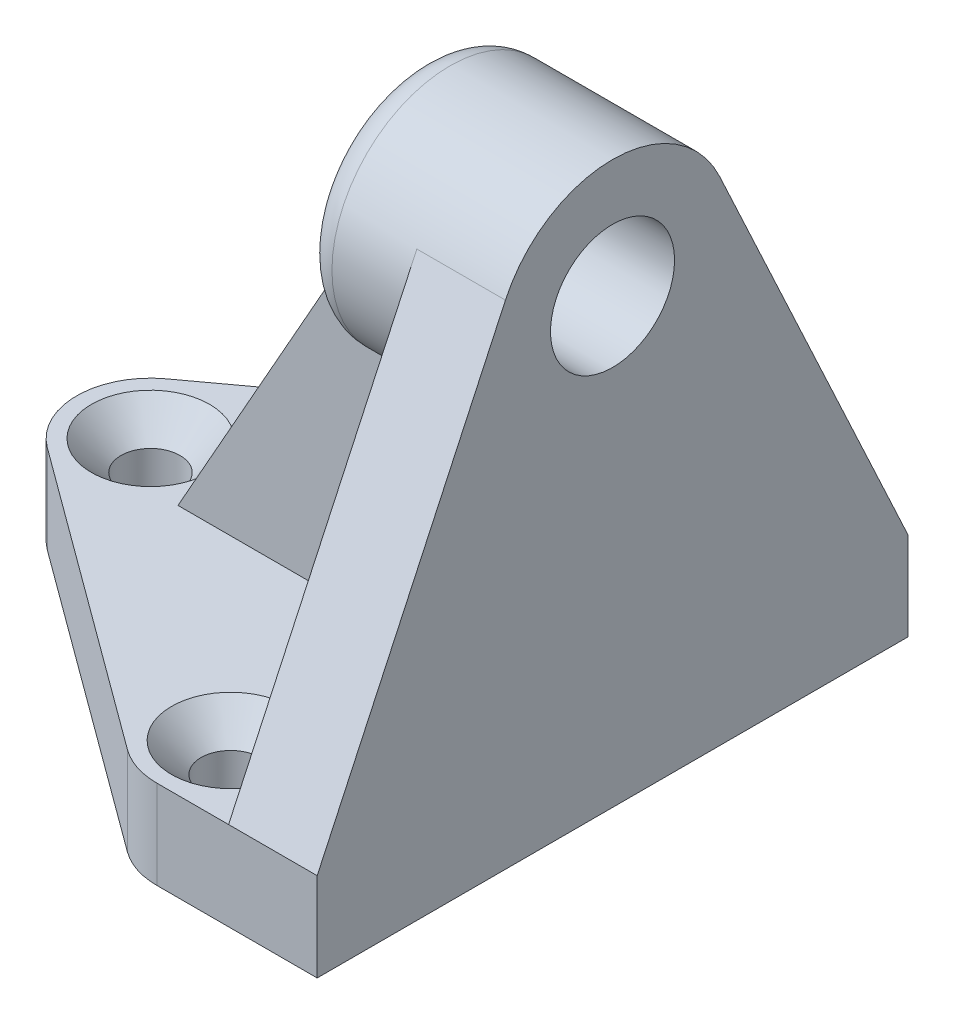
SolidWorks part; units mm, degrees
material "ABS"
ref_plane "Спереди" through (0, 0, 0) normal (0, 0, 1) x (1, 0, 0)
ref_plane "Сверху" through (0, 0, 0) normal (0, 1, 0) x (1, 0, 0)
ref_plane "Справа" through (0, 0, 0) normal (1, 0, 0) x (0, 0, -1)
other "Configuration Table"
sketch "Эскиз1" plane through (0, 0, 0) normal (0, 1, 0) x (1, 0, 0)
  line L0 (0, -20) -> (0, 20)
  line L4 (0, 0) -> (-50, 0) construction
  line L7 (0, -20) -> (-10.8613, -20)
  line L8 (0, 20) -> (-10.8613, 20)
  line L9 (-34.2466, -4.03) -> (-13.8208, -19.03)
  line L10 (-34.2466, 4.03) -> (-13.8208, 19.03)
  arc A1 (-34.2466, 4.03) -> (-34.2466, -4.03) centre (-31.2871, 0) ccw
  circle A4 centre (-31.2871, 0) radius 2
  circle A5 centre (-10.8613, -15) radius 2
  arc A6 (-10.8613, -20) -> (-13.8208, -19.03) centre (-10.8613, -15) cw
  arc A7 (-10.8613, 20) -> (-13.8208, 19.03) centre (-10.8613, 15) ccw
  circle A8 centre (-10.8613, 15) radius 2
  point P2 (0, 0)
  point P13 (-12.5, -20)
  point P16 (-12.5, 20)
  dimension "D3" = 12.5
  dimension "D4" = 5
  dimension "D6" = 5
  dimension "D7" = 4
  dimension "D8" = 4
  dimension "D9" = 5
  dimension "D10" = 4
  dimension "D11" = 10.8613
  dimension "D1" = 40
  dimension "D2" = 50
  dimension "D5" = 31.2871
extrude "Бобышка-Вытянуть1" add sketch "Эскиз1" along normal blind 6
chamfer "Фаска3" distance 2 angle 45 3 edges at (-10.8613, 6, 17) (-31.2871, 6, 2) (-10.8613, 6, -13)
sketch "Эскиз4" plane through (0, 0, 0) normal (1, 0, 0) x (0, 0, -1)
  line L0 (0, 0) -> (0, 53.5747) construction
  line L1 (-20, 0) -> (20, 0) construction
  line L2 (-45.2355, 6) -> (56.9604, 6) construction
  line L3 (-7.2523, 33.3769) -> (-20, 6)
  line L4 (-20, 6) -> (-20, 0) construction
  line L5 (7.2523, 33.3769) -> (20, 6)
  line L6 (-20, 6) -> (20, 6)
  arc A0 (7.2523, 33.3769) -> (-7.2523, 33.3769) centre (0, 30) ccw
  circle A1 centre (0, 30) radius 4.2
  dimension "D1" = 16
  dimension "D4" = 8.4
  dimension "D2" = 30
  dimension "D3" = 40
extrude "Бобышка-Вытянуть2" add sketch "Эскиз4" against normal blind 6
sketch "Эскиз7" plane through (-6, 0, 0) normal (-1, 0, 0) x (0, 0, 1)
  circle A0 centre (0, 30) radius 8
extrude "Бобышка-Вытянуть3" add sketch "Эскиз7" along normal blind 7
fillet "Скругление1" radius 2 1 edges at (-13, 30, 8)
sketch "Эскиз8" plane through (0, 0, 0) normal (0, 0, 1) x (1, 0, 0)
  line L0 (-6, 33.3769) -> (-6, 6) construction
  line L1 (-26.4271, 6) -> (-12.6069, 30.4867)
  line L2 (-34.2466, 6) -> (-13.8208, 6) construction
  line L3 (-26.4271, 6) -> (-4.2147, 6)
  line L4 (-6, 6) -> (0, 6) construction
  line L5 (-4.2147, 6) -> (-4.8089, 17.7344)
  line L6 (-4.8089, 17.7344) -> (-11.5303, 17.7344)
  line L7 (-11.5303, 17.7344) -> (-11.5303, 30.4867)
  line L8 (-11.5303, 30.4867) -> (-12.6069, 30.4867)
  dimension "D1" = 0.8613
  dimension "D2" = 0.86
extrude "Бобышка-Вытянуть4" add sketch "Эскиз8" along normal blind 3 and the other way blind 3
sketch "Эскиз9" plane through (0, 0, 0) normal (1, 0, 0) x (0, 0, -1)
  circle A0 centre (0, 30) radius 4.2
  dimension "D1" = 8.4
extrude "Вырез-Вытянуть1" cut sketch "Эскиз9" against normal blind 10
